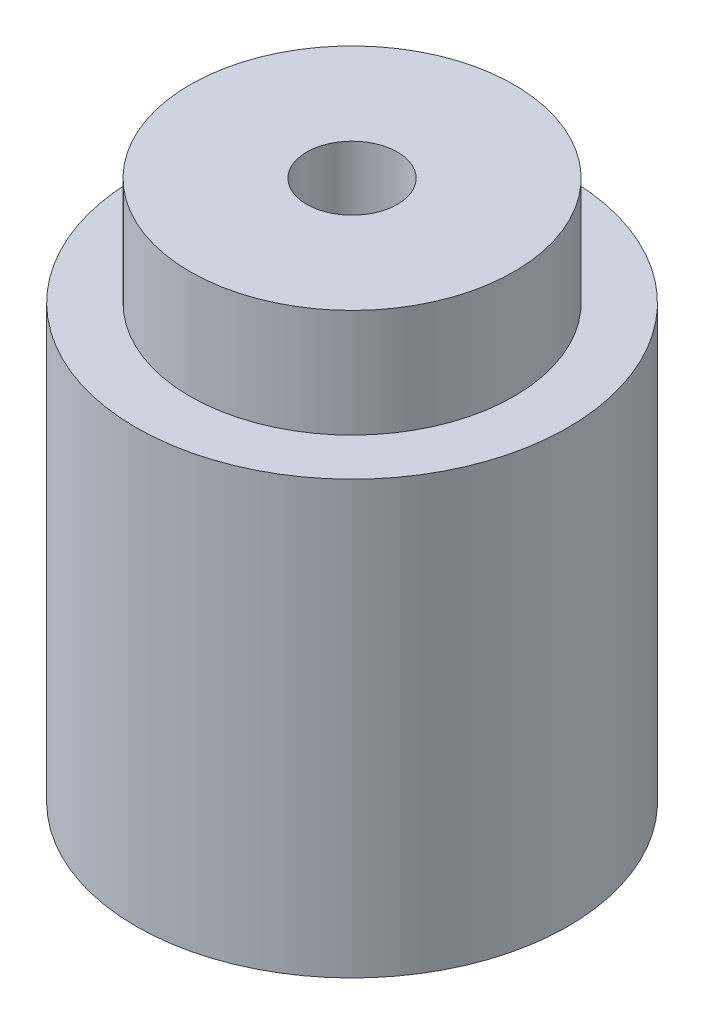
SolidWorks part; units mm, degrees
material "Brass"
ref_plane "Front Plane" through (0, 0, 0) normal (0, 0, 1) x (1, 0, 0)
ref_plane "Top Plane" through (0, 0, 0) normal (0, 1, 0) x (1, 0, 0)
ref_plane "Right Plane" through (0, 0, 0) normal (1, 0, 0) x (0, 0, -1)
sketch "Sketch1" plane through (0, 0, 0) normal (0, 1, 0) x (1, 0, 0)
  circle A4 centre (0, 0) radius 10
  dimension "D1" = 20
extrude "Boss-Extrude1" add sketch "Sketch1" along normal blind 25
sketch "Sketch4" plane through (0, 25, 0) normal (0, 1, 0) x (1, 0, 0)
  circle A0 centre (0, 0) radius 3
  dimension "D1" = 6
hole_wizard "M5 Tapped Hole1" positions "Sketch16" profile "Sketch17" tap size "M5" standard "ISO"
sketch "Sketch16" plane through (0, 25, 0) normal (0, 1, 0) x (1, 0, 0)
  point P0 (0, 0)
sketch "Sketch17" plane through (0, 25, 0) normal (1, 0, 0) x (0, 0, 1)
  line L0 (0, 0) -> (0, 15)
  line L1 (0, 15) -> (2.1, 13.7382)
  line L2 (2.1, 13.7382) -> (2.1, 0)
  line L5 (2.1, 0) -> (0, 0)
  line L10 (0, 15) -> (-2.1, 13.7382) construction
  line L11 (0, -6.35) -> (0, 107.95) construction
  dimension "Tap Drill Dia." = 4.2
  dimension "Tap Drill Depth" = 15
  dimension "Drill Angle" = 118
cosmetic thread "Hole Thread1" parameters "D1"=10, "D2"=5
sketch "Sketch18" plane through (0, 25, 0) normal (0, 1, 0) x (1, 0, 0)
  circle A0 centre (0, 0) radius 7.5
  circle A1 centre (0, 0) radius 10
  dimension "D1" = 15
  dimension "D2" = 20
extrude "Cut-Extrude1" cut sketch "Sketch18" against normal blind 5
